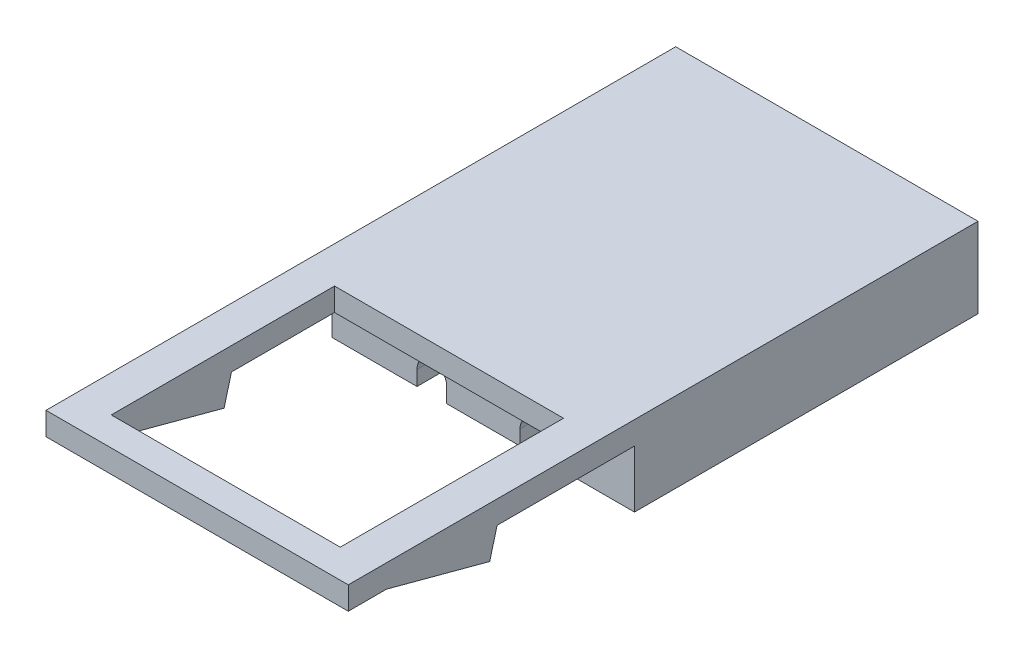
SolidWorks part; units mm, degrees
ref_plane "Front Plane" through (0, 0, 0) normal (0, 0, 1) x (1, 0, 0)
ref_plane "Top Plane" through (0, 0, 0) normal (0, 1, 0) x (1, 0, 0)
ref_plane "Right Plane" through (0, 0, 0) normal (1, 0, 0) x (0, 0, -1)
sketch "Sketch1" plane through (0, 0, 0) normal (0, 1, 0) x (1, 0, 0)
  line L1 (-31.75, 35) -> (31.75, 35)
  line L2 (-31.75, 35) -> (-31.75, 0)
  line L3 (-31.75, 0) -> (31.75, 0)
  line L4 (31.75, 35) -> (31.75, 0)
extrude "Boss-Extrude1" add sketch "Sketch1" along normal blind 12
sketch "Sketch3" plane through (0, 0, 0) normal (0, -1, 0) x (1, 0, 0)
  line L0 (-31.75, 0) -> (31.75, 0) construction
  line L1 (-13.2, 0) -> (13.2, 0)
  line L2 (-13.2, 0) -> (-13.2, -35)
  line L3 (-13.2, -35) -> (13.2, -35)
  line L4 (13.2, 0) -> (13.2, -35)
  line L5 (31.75, -35) -> (-31.75, -35) construction
extrude "Cut-Extrude2" cut sketch "Sketch3" against normal blind 5
sketch "Sketch4" plane through (0, 5, 0) normal (0, -1, 0) x (1, 0, 0)
  line L0 (13.2, 0) -> (-13.2, 0) construction
  line L1 (-5.8, 0) -> (-3.2, 0)
  line L2 (-5.8, 0) -> (-5.8, -35)
  line L3 (-5.8, -35) -> (-3.2, -35)
  line L4 (-3.2, 0) -> (-3.2, -35)
  line L5 (-13.2, -35) -> (13.2, -35) construction
  line L7 (3.2, 0) -> (5.8, 0)
  line L8 (3.2, 0) -> (3.2, -35)
  line L9 (3.2, -35) -> (5.8, -35)
  line L10 (5.8, 0) -> (5.8, -35)
extrude "Cut-Extrude3" cut sketch "Sketch4" against normal blind 1.3
sketch "Sketch5" plane through (0, 0, 0) normal (0, -1, 0) x (1, 0, 0)
  line L1 (-31.75, -35) -> (-13.2, -35)
  line L2 (-31.75, -35) -> (-31.75, 0)
  line L3 (-31.75, 0) -> (-13.2, 0)
  line L4 (-13.2, -35) -> (-13.2, 0)
extrude "Cut-Extrude4" cut sketch "Sketch5" against normal through all
sketch "Sketch6" plane through (0, 0, 0) normal (0, -1, 0) x (1, 0, 0)
  line L1 (13.2, 0) -> (31.75, 0)
  line L2 (13.2, 0) -> (13.2, -35)
  line L3 (13.2, -35) -> (31.75, -35)
  line L4 (31.75, 0) -> (31.75, -35)
extrude "Cut-Extrude5" cut sketch "Sketch6" against normal through all
sketch "Sketch7" plane through (0, 0, 0) normal (0, 0, 1) x (1, 0, 0)
  circle A0 centre (-9, 8.5) radius 2.5
extrude "Cut-Extrude6" cut sketch "Sketch7" against normal through all
sketch "Sketch8" plane through (0, 0, 0) normal (0, 0, 1) x (1, 0, 0)
  circle A0 centre (9, 8.5) radius 2.5
extrude "Cut-Extrude7" cut sketch "Sketch8" against normal through all
sketch "Sketch12" plane through (0, 0, 0) normal (0, 0, 1) x (1, 0, 0)
  line L0 (13.2, 12) -> (13.2, 5) construction
  line L1 (-13.2, 5) -> (13.2, 5)
  line L2 (-13.2, 5) -> (-13.2, 15)
  line L3 (-13.2, 15) -> (13.2, 15)
  line L4 (13.2, 5) -> (13.2, 15)
extrude "Boss-Extrude2" add sketch "Sketch12" along normal blind 27
sketch "Sketch13" plane through (0, 15, 0) normal (0, 1, 0) x (1, 0, 0)
  line L1 (10, -5) -> (-10, -5)
  line L2 (10, -5) -> (10, -24.5)
  line L3 (10, -24.5) -> (-10, -24.5)
  line L4 (-10, -5) -> (-10, -24.5)
extrude "Cut-Extrude8" cut sketch "Sketch13" against normal through all
sketch "Sketch14" plane through (-13.2, 0, 0) normal (-1, 0, 0) x (0, 0, 1)
  line L1 (0, 12) -> (27, 12)
  line L2 (0, 12) -> (0, 15)
  line L3 (0, 15) -> (27, 15)
  line L4 (27, 12) -> (27, 15)
extrude "Cut-Extrude9" cut sketch "Sketch14" against normal through all
sketch "Sketch18" plane through (0, 0, 0) normal (0, 0, -1) x (-1, 0, 0)
  line L1 (3.2, 6.3) -> (5.8, 6.3)
  line L2 (3.2, 6.3) -> (3.2, 5)
  line L3 (3.2, 5) -> (5.8, 5)
  line L4 (5.8, 6.3) -> (5.8, 5)
  line L5 (-5.8, 6.3) -> (-3.2, 6.3)
  line L6 (-5.8, 6.3) -> (-5.8, 5)
  line L7 (-5.8, 5) -> (-3.2, 5)
  line L8 (-3.2, 6.3) -> (-3.2, 5)
extrude "Cut-Extrude12" cut sketch "Sketch18" against normal through all
sketch "Sketch19" plane through (-13.2, 0, 0) normal (-1, 0, 0) x (0, 0, 1)
  line L0 (27, 5) -> (-35, 5) construction
  line L1 (4, 5) -> (14, 5)
  line L2 (4, 5) -> (4, 10)
  line L3 (4, 10) -> (14, 10)
  line L4 (14, 5) -> (14, 10)
extrude "Cut-Extrude13" cut sketch "Sketch19" against normal through all
sketch "Sketch20" plane through (-13.2, 0, 0) normal (-1, 0, 0) x (0, 0, 1)
  line L0 (27, 12) -> (27, 5) construction
  line L1 (27, 10) -> (24.5, 10)
  line L2 (27, 10) -> (27, 5)
  line L3 (27, 5) -> (24.5, 5)
  line L4 (24.5, 10) -> (24.5, 5)
  line L5 (27, 5) -> (14, 5) construction
extrude "Cut-Extrude14" cut sketch "Sketch20" against normal through all
sketch "Sketch21" plane through (-13.2, 0, 0) normal (-1, 0, 0) x (0, 0, 1)
  line L0 (14, 10) -> (14.647, 7.5852)
  line L1 (14.647, 7.5852) -> (23.6593, 10)
  line L2 (24.5, 10) -> (24.5, 5)
  line L3 (24.5, 5) -> (14, 5)
  line L4 (14, 5) -> (14, 10)
  line L5 (23.6593, 10) -> (24.5, 10)
extrude "Cut-Extrude15" cut sketch "Sketch21" against normal through all
sketch "Sketch24" plane through (0, 5, 0) normal (0, -1, 0) x (1, 0, 0)
  line L0 (13.2, -35) -> (13.2, 4) construction
  line L1 (-13.2, 4) -> (13.2, 4)
  line L2 (-13.2, 4) -> (-13.2, 2)
  line L3 (-13.2, 2) -> (13.2, 2)
  line L4 (13.2, 4) -> (13.2, 2)
extrude "Cut-Extrude18" cut sketch "Sketch24" against normal blind 5
sketch "Sketch25" plane through (0, 12, 0) normal (0, 1, 0) x (1, 0, 0)
  line L0 (-13.2, 35) -> (-13.2, -27) construction
  line L1 (13.2, 35) -> (-13.2, 35)
  line L2 (13.2, 35) -> (13.2, 28)
  line L3 (13.2, 28) -> (-13.2, 28)
  line L5 (-13.2, 35) -> (-13.2, 28)
extrude "Cut-Extrude19" cut sketch "Sketch25" against normal through all
sketch "Sketch26" plane through (0, 0, -28) normal (0, 0, -1) x (-1, 0, 0)
  circle A0 centre (4.5, 6.3) radius 1.3
  circle A1 centre (-4.5, 6.3) radius 1.3
extrude "Cut-Extrude20" cut sketch "Sketch26" against normal through all
